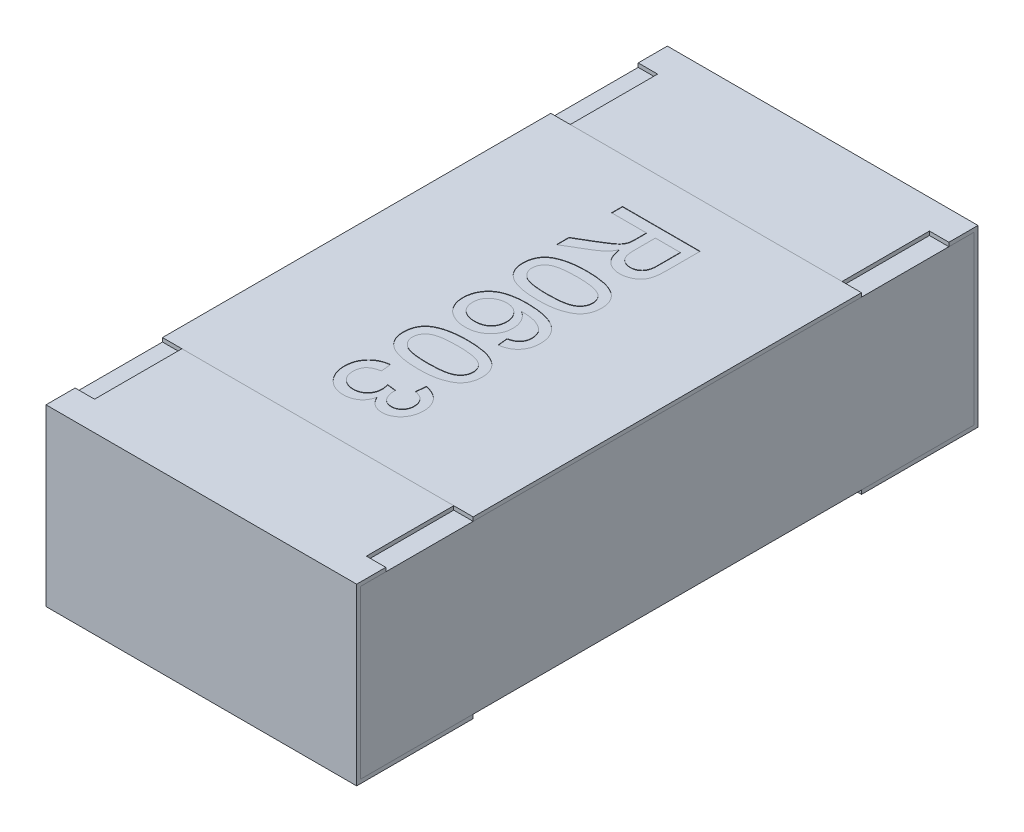
SolidWorks part; units mm, degrees
ref_plane "Front Plane" through (0, 0, 0) normal (0, 0, 1) x (1, 0, 0)
ref_plane "Top Plane" through (0, 0, 0) normal (0, 1, 0) x (1, 0, 0)
ref_plane "Right Plane" through (0, 0, 0) normal (1, 0, 0) x (0, 0, -1)
sketch "Sketch4" plane through (0, 0, 0) normal (1, 0, 0) x (0, 0, -1)
  line L0 (0, 0.1169) -> (0, -0.0721) construction
  line L1 (-0.8, 0) -> (0.3788, 0) construction
  line L2 (-0.8, 0.225) -> (-0.8, -0.225)
  line L3 (-0.8, -0.225) -> (-0.5, -0.225)
  line L4 (-0.5, 0.225) -> (-0.5, 0.215)
  line L5 (-0.5, 0.215) -> (-0.79, 0.215)
  line L6 (-0.79, 0.215) -> (-0.79, -0.215)
  line L7 (-0.79, -0.215) -> (-0.5, -0.215)
  line L8 (-0.5, -0.215) -> (-0.5, -0.225)
  line L9 (-0.5, 0.225) -> (-0.8, 0.225)
  line L10 (0.5, 0.225) -> (0.8, 0.225)
  line L11 (0.5, -0.215) -> (0.5, -0.225)
  line L12 (0.79, -0.215) -> (0.5, -0.215)
  line L13 (0.79, 0.215) -> (0.79, -0.215)
  line L14 (0.5, 0.215) -> (0.79, 0.215)
  line L15 (0.5, 0.225) -> (0.5, 0.215)
  line L16 (0.8, -0.225) -> (0.5, -0.225)
  line L17 (0.8, 0.225) -> (0.8, -0.225)
  dimension "LENGTH" = 0.8
  dimension "HEIGHT" = 0.45
  dimension "END CAP TOP LENGTH" = 0.3
  dimension "END CAP BOTTOM LENGTH" = 0.3
  dimension "D5" = 0.01
  dimension "D6" = 0.01
extrude "Boss-Extrude2" add sketch "Sketch4" along normal mid plane 0.8
sketch "Sketch5" plane through (0, 0, 0) normal (1, 0, 0) x (0, 0, -1)
  line L1 (-0.79, 0.215) -> (0.79, 0.215)
  line L2 (-0.79, 0.215) -> (-0.79, -0.215)
  line L3 (-0.79, -0.215) -> (0.79, -0.215)
  line L4 (0.79, 0.215) -> (0.79, -0.215)
extrude "Boss-Extrude3" add sketch "Sketch5" along normal up to surface and the other way up to surface separate body
sketch "Sketch6" plane through (0, 0.225, 0) normal (0, 1, 0) x (1, 0, 0)
  line L0 (-0.4, 0.8) -> (-0.4, 0.5) construction
  line L1 (-0.4, 0.725) -> (-0.35, 0.725)
  line L2 (-0.4, 0.725) -> (-0.4, 0.5)
  line L3 (-0.4, 0.5) -> (-0.35, 0.5)
  line L4 (-0.35, 0.725) -> (-0.35, 0.5)
  line L5 (0.4, 0.5) -> (-0.4, 0.5) construction
  line L6 (0, 0.0345) -> (0, -0.0345) construction
  line L7 (-0.0325, 0) -> (0.03, 0) construction
  line L8 (0.4, 0.725) -> (0.4, 0.5)
  line L9 (0.4, 0.5) -> (0.35, 0.5)
  line L10 (0.35, 0.725) -> (0.35, 0.5)
  line L11 (0.4, 0.725) -> (0.35, 0.725)
  line L12 (0.4, -0.725) -> (0.35, -0.725)
  line L13 (0.4, -0.725) -> (0.4, -0.5)
  line L14 (0.4, -0.5) -> (0.35, -0.5)
  line L15 (0.35, -0.725) -> (0.35, -0.5)
  line L16 (-0.4, -0.725) -> (-0.35, -0.725)
  line L17 (-0.4, -0.725) -> (-0.4, -0.5)
  line L18 (-0.4, -0.5) -> (-0.35, -0.5)
  line L19 (-0.35, -0.725) -> (-0.35, -0.5)
  dimension "TOP CUT WIDTH" = 0.05
  dimension "TOP CUT LENGTH" = 0.225
extrude "Cut-Extrude1" cut sketch "Sketch6" against normal up to surface (0.01 mm away) up to face at (0, 0.215, 0)
sketch "Sketch7" plane through (0, 0.215, 0) normal (0, 1, 0) x (1, 0, 0)
  line L1 (-0.4, 0.5) -> (0.4, 0.5)
  line L2 (-0.4, 0.5) -> (-0.4, -0.5)
  line L3 (-0.4, -0.5) -> (0.4, -0.5)
  line L4 (0.4, 0.5) -> (0.4, -0.5)
  line L5 (0.35, -0.5) -> (-0.35, -0.5) construction
  line L6 (0.35, 0.5) -> (-0.35, 0.5) construction
  line L7 (-0.4, -0.79) -> (-0.4, 0.79) construction
  line L8 (0.4, 0.79) -> (0.4, -0.79) construction
extrude "Boss-Extrude4" add sketch "Sketch7" along normal up to surface (0.01 mm away) separate body up to face at (0, 0.225, -0.6875)
sketch "Sketch10" plane through (0, 0.225, 0) normal (0, 1, 0) x (1, 0, 0)
  line L0 (-0.1, 0.425) -> (-0.1, -0.425) construction
  line L1 (0, 0) -> (-0.1, 0) construction
  text T0 "R0603" font "Arial" height 0.2
  dimension "D1" = 0.1
  dimension "D2" = 0.85
extrude "TEXT0603" cut sketch "Sketch10" against normal blind 0.001
